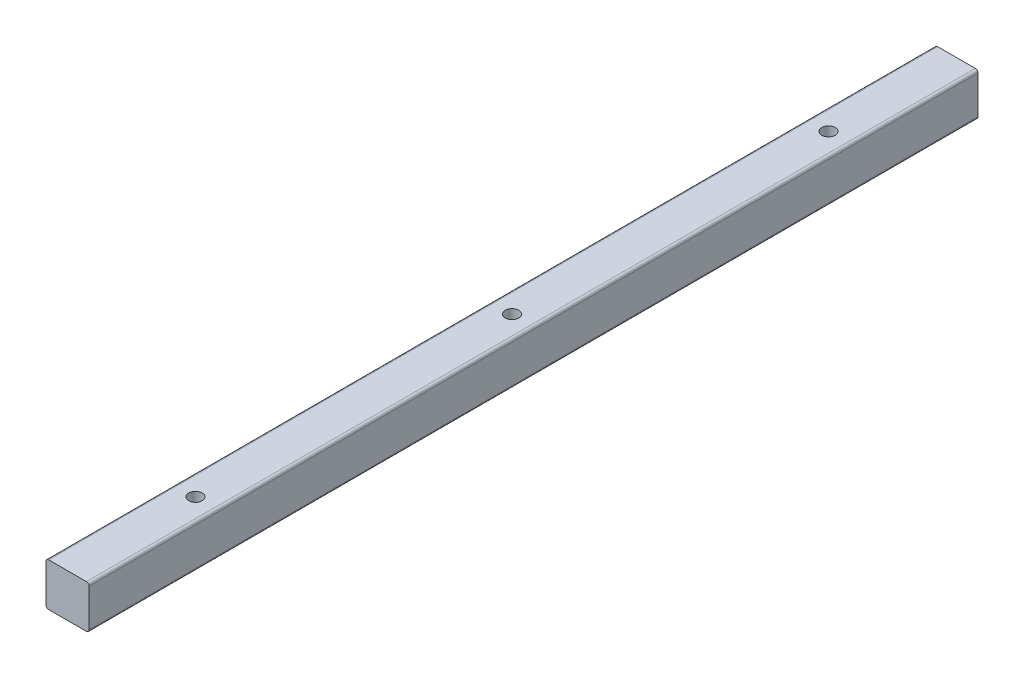
SolidWorks part; units mm, degrees
material "XC38"
ref_plane "Face" through (0, 0, 0) normal (0, 0, 1) x (1, 0, 0)
ref_plane "Dessus" through (0, 0, 0) normal (0, 1, 0) x (1, 0, 0)
ref_plane "Droite" through (0, 0, 0) normal (1, 0, 0) x (0, 0, -1)
sketch "Esquisse1" plane through (0, 0, 0) normal (0, 0, 1) x (1, 0, 0)
  line L1 (7, 8) -> (-7, 8)
  line L2 (8, 7) -> (8, -7)
  line L3 (7, -8) -> (-7, -8)
  line L4 (-8, 7) -> (-8, -7)
  line L5 (8, 8) -> (-8, -8) construction
  line L6 (8, -8) -> (-8, 8) construction
  arc A0 (-7, -8) -> (-8, -7) centre (-7, -7) cw
  arc A1 (8, -7) -> (7, -8) centre (7, -7) cw
  arc A2 (7, 8) -> (8, 7) centre (7, 7) cw
  arc A3 (-7, 8) -> (-8, 7) centre (-7, 7) ccw
  point P0 (0, 0)
  dimension "D2" = 1
  dimension "D1" = 16
extrude "Boss.-Extru.1" add sketch "Esquisse1" along normal mid plane 330
hole_wizard "Trou taraudé M61" positions "Esquisse3" profile "Esquisse2" tap size "M6" standard "ISO"
sketch "Esquisse3" plane through (0, 8, 0) normal (0, 1, 0) x (1, 0, 0)
  line L0 (0, 117.5) -> (0, -117.5) construction
  point P0 (0, 0)
  point P3 (0, 117.5)
  point P5 (0, -117.5)
  dimension "D1" = 235
sketch "Esquisse2" plane through (0, 8, 0) normal (1, 0, 0) x (0, 0, 1)
  line L0 (0, 0) -> (0, 14.5022)
  line L1 (0, 14.5022) -> (2.5, 13)
  line L2 (2.5, 13) -> (2.5, 0)
  line L5 (2.5, 0) -> (0, 0)
  line L10 (0, 14.5022) -> (-2.5, 13) construction
  line L11 (0, -6.35) -> (0, 107.95) construction
  dimension "Diamètre du trou pour taraudage" = 5
  dimension "Profondeur du trou pour taraudage" = 13
  dimension "Angle de pointe" = 118
cosmetic thread "Filetage de perçage1" parameters "D1"=10, "D2"=6
cosmetic thread "Filetage de perçage2" parameters "D1"=10, "D2"=6
cosmetic thread "Filetage de perçage3" parameters "D1"=10, "D2"=6
hole_wizard "Trou taraudé M31" positions "Esquisse5" profile "Esquisse4" tap size "M3" standard "ISO"
sketch "Esquisse5" plane through (0, -8, 0) normal (0, -1, 0) x (-1, 0, 0)
  point P0 (0, 10)
  point P3 (0, 50)
  dimension "D1" = 40
  dimension "D2" = 10
sketch "Esquisse4" plane through (0, -8, -10) normal (1, 0, 0) x (0, 0, -1)
  line L0 (0, 0) -> (0, 9.2511)
  line L1 (0, 9.2511) -> (1.25, 8.5)
  line L2 (1.25, 8.5) -> (1.25, 0)
  line L5 (1.25, 0) -> (0, 0)
  line L10 (0, 9.2511) -> (-1.25, 8.5) construction
  line L11 (0, -6.35) -> (0, 107.95) construction
  dimension "Diamètre du trou pour taraudage" = 2.5
  dimension "Profondeur du trou pour taraudage" = 8.5
  dimension "Angle de pointe" = 118
cosmetic thread "Filetage de perçage4" parameters "D1"=6, "D2"=3
cosmetic thread "Filetage de perçage5" parameters "D1"=3, "D2"=3
